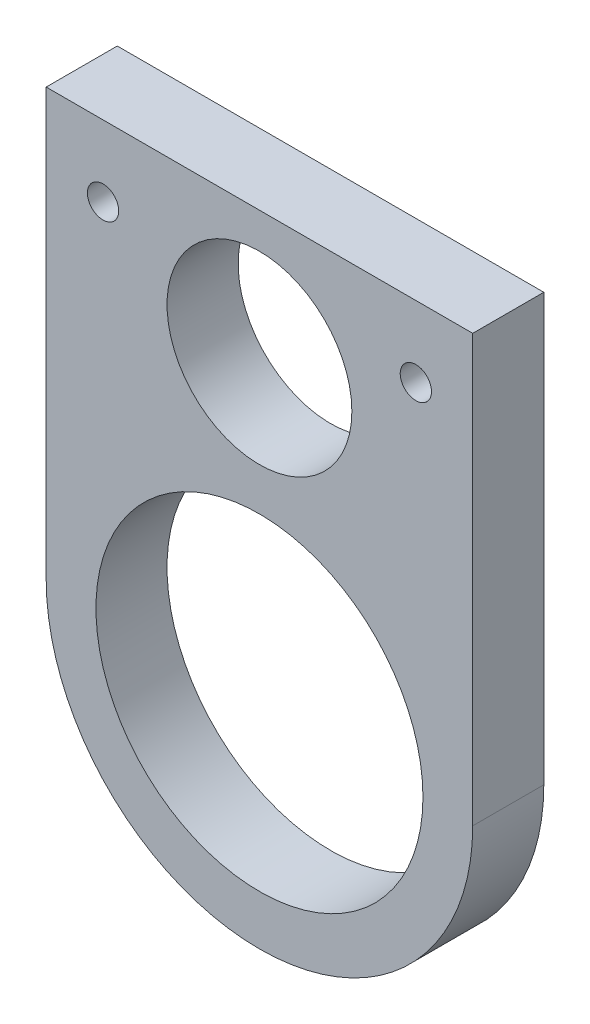
SolidWorks part; units mm, degrees
material "6061-T6 (SS)"
ref_plane "Front Plane" through (0, 0, 0) normal (0, 0, 1) x (1, 0, 0)
ref_plane "Top Plane" through (0, 0, 0) normal (0, 1, 0) x (1, 0, 0)
ref_plane "Right Plane" through (0, 0, 0) normal (1, 0, 0) x (0, 0, -1)
sketch "Sketch1" plane through (0, 0, 0) normal (0, 0, 1) x (1, 0, 0)
  line L0 (0, 0) -> (38.1, 0)
  line L1 (38.1, -38.1) -> (38.1, 0)
  line L2 (0, 0) -> (0, -38.1)
  arc A0 (0, -38.1) -> (38.1, -38.1) centre (19.05, -38.1) ccw
  point P6 (24.1029, 0)
  dimension "D1" = 19.05
  dimension "D2" = 38.1
extrude "Boss-Extrude1" add sketch "Sketch1" along normal blind 6.35
sketch "Sketch2" plane through (0, 0, 6.35) normal (0, 0, 1) x (1, 0, 0)
  line L3 (0, 0) -> (0, -38.1)
  line L4 (38.1, -38.1) -> (38.1, 0)
  line L5 (38.1, 0) -> (0, 0)
  line L6 (0, 0) -> (0, -38.1) construction
  line L7 (38.1, -38.1) -> (38.1, 0)
  line L8 (38.1, 0) -> (0, 0)
  circle A0 centre (19.05, -38.1) radius 14.605
  arc A1 (0, -38.1) -> (38.1, -38.1) centre (19.05, -38.1) ccw
  arc A2 (0, -38.1) -> (38.1, -38.1) centre (19.05, -38.1) ccw construction
  circle A3 centre (19.05, -10.16) radius 7.62
  dimension "D2" = 29.21
  dimension "D4" = 15.24
  dimension "D3" = 27.94
  dimension "D1" = 0
extrude "Cut-Extrude3" cut sketch "Sketch2" against normal blind 6.35 contours A0
sketch "Sketch3" plane through (0, 0, 6.35) normal (0, 0, 1) x (1, 0, 0)
  circle A0 centre (19.05, -38.1) radius 14.605 construction
  circle A1 centre (19.05, -38.1) radius 14.605 construction
  circle A2 centre (19.05, -11.43) radius 8.255
  dimension "D1" = 16.51
  dimension "D2" = 26.67
extrude "Cut-Extrude4" cut sketch "Sketch3" against normal blind 6.35
ref_plane "Plane1" through (0, 2.54, 0) normal (0, 1, 0) x (1, 0, 0)
ref_point "Point1"
ref_point "Point2"
sketch "Sketch5" plane through (0, 0, 6.35) normal (0, 0, 1) x (1, 0, 0)
  circle A0 centre (5.08, -6.35) radius 1.397
  circle A1 centre (33.02, -6.35) radius 1.397
  dimension "D5" = 2.794
  dimension "D6" = 2.794
  dimension "D1" = 6.35
  dimension "D2" = 5.08
  dimension "D3" = 6.35
  dimension "D4" = 5.08
extrude "Cut-Extrude5" cut sketch "Sketch5" against normal blind 6.35
